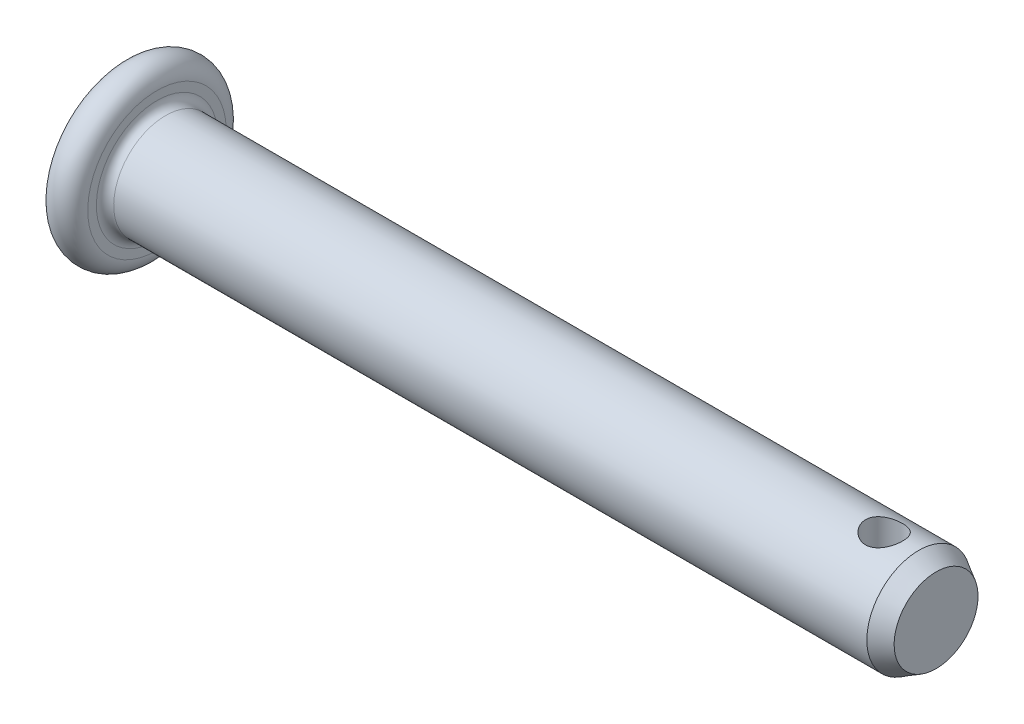
SolidWorks part; units mm, degrees
ref_plane "Front" through (0, 0, 0) normal (0, 0, 1) x (1, 0, 0)
ref_plane "Top" through (0, 0, 0) normal (0, 1, 0) x (1, 0, 0)
ref_plane "Right" through (0, 0, 0) normal (1, 0, 0) x (0, 0, -1)
sketch "Sketch1" plane through (0, 0, 0) normal (0, 0, 1) x (1, 0, 0)
  line L0 (47, 0) -> (0, 0)
  line L1 (0, 0) -> (0, 4)
  line L2 (47, 0) -> (47, 2.4226)
  line L3 (47, 2.4226) -> (46, 3)
  line L4 (46, 3) -> (2, 3)
  line L5 (2, 3) -> (2, 4)
  line L6 (-19.83, 0) -> (9.2989, 0) construction
  arc A0 (0, 4) -> (2, 4) centre (1, 4) cw
  dimension "l" = 45
  dimension "k" = 2
  dimension "d" = 6
  dimension "D4" = 30
  dimension "c" = 1
  dimension "dk" = 10
revolve "BaseBody" add sketch "Sketch1" angle 360 about L6
fillet "Chamfer1" radius 0.5 1 edges at (2, -3, 0)
sketch "Sketch2" plane through (0, 0, 0) normal (0, 1, 0) x (1, 0, 0)
  line L0 (-19.83, 0) -> (9.2989, 0) construction
  line L1 (47, -2.4226) -> (47, 2.4226) construction
  circle A0 centre (44, 0) radius 1.07
  dimension "D2" = 3
  dimension "d1" = 2.14
extrude "Hole" cut sketch "Sketch2" against normal through all and the other way through all
